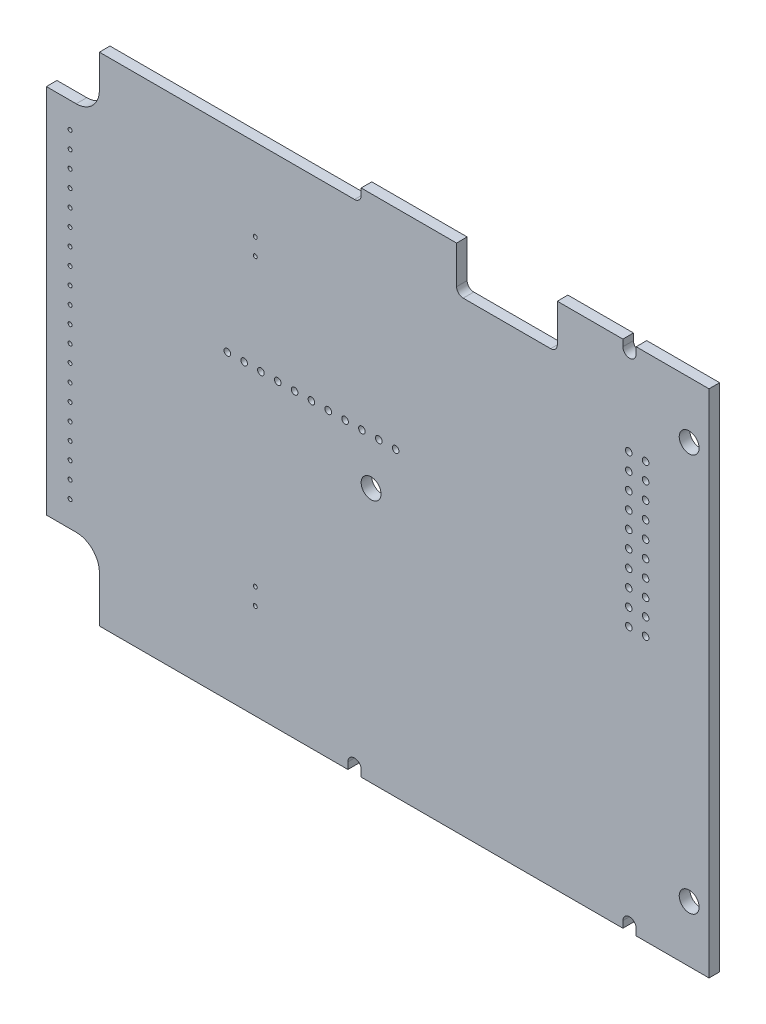
SolidWorks part; units mm, degrees
ref_plane "Płaszczyzna przednia" through (0, 0, 0) normal (0, 0, 1) x (1, 0, 0)
ref_plane "Płaszczyzna górna" through (0, 0, 0) normal (0, 1, 0) x (1, 0, 0)
ref_plane "Płaszczyzna prawa" through (0, 0, 0) normal (1, 0, 0) x (0, 0, -1)
sketch "Geometry Import" plane through (0, 0, 0) normal (0, 0, 1) x (1, 0, 0)
  line L0 (246.9504, 64.1305) -> (246.9504, 64.6805) construction
  line L1 (245.4504, 64.6805) -> (245.4504, 64.1305) construction
  line L2 (245.4504, 64.1305) -> (246.9504, 64.1305) construction
  line L3 (245.4504, 64.1305) -> (245.4504, 63.0305) construction
  line L4 (245.9504, 62.5305) -> (246.9504, 62.5305) construction
  line L5 (246.9504, 62.5305) -> (246.9504, 64.1305) construction
  line L6 (246.9504, 64.1305) -> (245.4504, 64.1305) construction
  line L7 (293.2004, 64.1305) -> (293.2004, 64.6805) construction
  line L8 (291.7004, 64.6805) -> (291.7004, 64.1305) construction
  line L9 (291.7004, 64.1305) -> (293.2004, 64.1305) construction
  line L10 (291.7004, 63.1805) -> (293.2004, 63.1805) construction
  line L11 (293.2004, 63.1805) -> (293.2004, 64.1305) construction
  line L12 (293.2004, 64.1305) -> (291.7004, 64.1305) construction
  line L13 (291.7004, 64.1305) -> (291.7004, 63.1805) construction
  line L14 (334.7004, 64.1305) -> (334.7004, 64.6805) construction
  line L15 (333.2004, 64.6805) -> (333.2004, 64.1305) construction
  line L16 (333.2004, 64.1305) -> (334.7004, 64.1305) construction
  line L17 (333.2004, 63.1805) -> (334.7004, 63.1805) construction
  line L18 (334.7004, 63.1805) -> (334.7004, 64.1305) construction
  line L19 (334.7004, 64.1305) -> (333.2004, 64.1305) construction
  line L20 (333.2004, 64.1305) -> (333.2004, 63.1805) construction
  line L21 (376.2004, 64.1305) -> (376.2004, 64.6805) construction
  line L22 (374.7004, 64.6805) -> (374.7004, 64.1305) construction
  line L23 (374.7004, 64.1305) -> (376.2004, 64.1305) construction
  line L24 (374.7004, 63.1805) -> (376.2004, 63.1805) construction
  line L25 (376.2004, 63.1805) -> (376.2004, 64.1305) construction
  line L26 (376.2004, 64.1305) -> (374.7004, 64.1305) construction
  line L27 (374.7004, 64.1305) -> (374.7004, 63.1805) construction
  line L28 (393.4504, 57.9305) -> (393.4504, 56.4305) construction
  line L29 (393.4504, 56.4305) -> (394.4004, 56.4305) construction
  line L30 (394.4004, 56.4305) -> (394.4004, 57.9305) construction
  line L31 (394.4004, 57.9305) -> (393.4504, 57.9305) construction
  line L32 (394.4004, 56.4305) -> (394.9504, 56.4305) construction
  line L33 (394.9504, 57.9305) -> (394.4004, 57.9305) construction
  line L34 (394.4004, 57.9305) -> (394.4004, 56.4305) construction
  line L35 (394.4004, -6.5695) -> (394.9504, -6.5695) construction
  line L36 (394.9504, -5.0695) -> (394.4004, -5.0695) construction
  line L37 (394.4004, -5.0695) -> (394.4004, -6.5695) construction
  line L38 (393.4504, -5.0695) -> (393.4504, -6.5695) construction
  line L39 (393.4504, -6.5695) -> (394.4004, -6.5695) construction
  line L40 (394.4004, -6.5695) -> (394.4004, -5.0695) construction
  line L41 (394.4004, -5.0695) -> (393.4504, -5.0695) construction
  line L42 (376.2004, -11.8195) -> (374.7004, -11.8195) construction
  line L43 (374.7004, -11.8195) -> (374.7004, -12.7695) construction
  line L44 (374.7004, -12.7695) -> (376.2004, -12.7695) construction
  line L45 (376.2004, -12.7695) -> (376.2004, -11.8195) construction
  line L46 (374.7004, -12.7695) -> (374.7004, -13.3195) construction
  line L47 (376.2004, -13.3195) -> (376.2004, -12.7695) construction
  line L48 (376.2004, -12.7695) -> (374.7004, -12.7695) construction
  line L49 (334.7004, -11.8195) -> (333.2004, -11.8195) construction
  line L50 (333.2004, -11.8195) -> (333.2004, -12.7695) construction
  line L51 (333.2004, -12.7695) -> (334.7004, -12.7695) construction
  line L52 (334.7004, -12.7695) -> (334.7004, -11.8195) construction
  line L53 (333.2004, -12.7695) -> (333.2004, -13.3195) construction
  line L54 (334.7004, -13.3195) -> (334.7004, -12.7695) construction
  line L55 (334.7004, -12.7695) -> (333.2004, -12.7695) construction
  line L56 (293.2004, -11.8195) -> (291.7004, -11.8195) construction
  line L57 (291.7004, -11.8195) -> (291.7004, -12.7695) construction
  line L58 (291.7004, -12.7695) -> (293.2004, -12.7695) construction
  line L59 (293.2004, -12.7695) -> (293.2004, -11.8195) construction
  line L60 (291.7004, -12.7695) -> (291.7004, -13.3195) construction
  line L61 (293.2004, -13.3195) -> (293.2004, -12.7695) construction
  line L62 (293.2004, -12.7695) -> (291.7004, -12.7695) construction
  line L63 (245.4504, -12.7695) -> (245.4504, -13.3195) construction
  line L64 (246.9504, -13.3195) -> (246.9504, -12.7695) construction
  line L65 (246.9504, -12.7695) -> (245.4504, -12.7695) construction
  line L66 (246.9504, -11.1695) -> (245.9504, -11.1695) construction
  line L67 (245.4504, -11.6695) -> (245.4504, -12.7695) construction
  line L68 (245.4504, -12.7695) -> (246.9504, -12.7695) construction
  line L69 (246.9504, -12.7695) -> (246.9504, -11.1695) construction
  line L70 (307.8504, 66.3305) -> (307.8504, 64.6805) construction
  line L71 (307.8504, 64.6805) -> (323.0504, 64.6805) construction
  line L72 (323.0504, 64.6805) -> (323.0504, 66.3305) construction
  line L73 (323.0504, 66.3305) -> (307.8504, 66.3305) construction
  line L74 (307.8504, 64.6805) -> (307.8504, 65.8305) construction
  line L75 (307.8504, 65.8305) -> (293.2004, 65.8305) construction
  line L76 (293.2004, 65.8305) -> (291.7004, 65.8305) construction
  line L77 (291.7004, 65.8305) -> (246.9504, 65.8305) construction
  line L78 (246.9504, 65.8305) -> (245.4504, 65.8305) construction
  line L79 (245.4504, 65.8305) -> (245.4504, 64.6805) construction
  line L80 (246.9504, 64.6805) -> (291.7004, 64.6805) construction
  line L81 (293.2004, 64.6805) -> (307.8504, 64.6805) construction
  line L82 (333.2004, 65.8305) -> (323.0504, 65.8305) construction
  line L83 (323.0504, 65.8305) -> (323.0504, 64.6805) construction
  line L84 (323.0504, 64.6805) -> (333.2004, 64.6805) construction
  line L85 (334.7004, 64.6805) -> (374.7004, 64.6805) construction
  line L86 (376.2004, 64.6805) -> (390.9504, 64.6805) construction
  line L87 (394.9504, 60.6805) -> (394.9504, 57.9305) construction
  line L88 (394.9504, 56.4305) -> (394.9504, -5.0695) construction
  line L89 (394.9504, -6.5695) -> (394.9504, -9.3195) construction
  line L90 (390.9504, -13.3195) -> (376.2004, -13.3195) construction
  line L91 (374.7004, -13.3195) -> (334.7004, -13.3195) construction
  line L92 (333.2004, -13.3195) -> (293.2004, -13.3195) construction
  line L93 (291.7004, -13.3195) -> (246.9504, -13.3195) construction
  line L94 (245.4504, -13.3195) -> (245.4504, -14.4695) construction
  line L95 (245.4504, -14.4695) -> (246.9504, -14.4695) construction
  line L96 (246.9504, -14.4695) -> (291.7004, -14.4695) construction
  line L97 (291.7004, -14.4695) -> (293.2004, -14.4695) construction
  line L98 (293.2004, -14.4695) -> (333.2004, -14.4695) construction
  line L99 (333.2004, -14.4695) -> (334.7004, -14.4695) construction
  line L100 (334.7004, -14.4695) -> (374.7004, -14.4695) construction
  line L101 (374.7004, -14.4695) -> (376.2004, -14.4695) construction
  line L102 (376.2004, -14.4695) -> (390.9504, -14.4695) construction
  line L103 (396.1004, -9.3195) -> (396.1004, -6.5695) construction
  line L104 (396.1004, -6.5695) -> (396.1004, -5.0695) construction
  line L105 (396.1004, -5.0695) -> (396.1004, 56.4305) construction
  line L106 (396.1004, 56.4305) -> (396.1004, 57.9305) construction
  line L107 (396.1004, 57.9305) -> (396.1004, 60.6805) construction
  line L108 (390.9504, 65.8305) -> (376.2004, 65.8305) construction
  line L109 (376.2004, 65.8305) -> (374.7004, 65.8305) construction
  line L110 (374.7004, 65.8305) -> (334.7004, 65.8305) construction
  line L111 (334.7004, 65.8305) -> (333.2004, 65.8305) construction
  line L112 (246.9504, 64.1305) -> (246.9504, 64.6805) construction
  line L113 (245.4504, 64.6805) -> (245.4504, 64.1305) construction
  line L114 (245.4504, 64.1305) -> (246.9504, 64.1305) construction
  line L115 (245.4504, 64.1305) -> (245.4504, 63.0305) construction
  line L116 (245.9504, 62.5305) -> (246.9504, 62.5305) construction
  line L117 (246.9504, 62.5305) -> (246.9504, 64.1305) construction
  line L118 (246.9504, 64.1305) -> (245.4504, 64.1305) construction
  line L119 (293.2004, 64.1305) -> (293.2004, 64.6805) construction
  line L120 (291.7004, 64.6805) -> (291.7004, 64.1305) construction
  line L121 (291.7004, 64.1305) -> (293.2004, 64.1305) construction
  line L122 (291.7004, 63.1805) -> (293.2004, 63.1805) construction
  line L123 (293.2004, 63.1805) -> (293.2004, 64.1305) construction
  line L124 (293.2004, 64.1305) -> (291.7004, 64.1305) construction
  line L125 (291.7004, 64.1305) -> (291.7004, 63.1805) construction
  line L126 (334.7004, 64.1305) -> (334.7004, 64.6805) construction
  line L127 (333.2004, 64.6805) -> (333.2004, 64.1305) construction
  line L128 (333.2004, 64.1305) -> (334.7004, 64.1305) construction
  line L129 (333.2004, 63.1805) -> (334.7004, 63.1805) construction
  line L130 (334.7004, 63.1805) -> (334.7004, 64.1305) construction
  line L131 (334.7004, 64.1305) -> (333.2004, 64.1305) construction
  line L132 (333.2004, 64.1305) -> (333.2004, 63.1805) construction
  line L133 (376.2004, 64.1305) -> (376.2004, 64.6805) construction
  line L134 (374.7004, 64.6805) -> (374.7004, 64.1305) construction
  line L135 (374.7004, 64.1305) -> (376.2004, 64.1305) construction
  line L136 (374.7004, 63.1805) -> (376.2004, 63.1805) construction
  line L137 (376.2004, 63.1805) -> (376.2004, 64.1305) construction
  line L138 (376.2004, 64.1305) -> (374.7004, 64.1305) construction
  line L139 (374.7004, 64.1305) -> (374.7004, 63.1805) construction
  line L140 (393.4504, 57.9305) -> (393.4504, 56.4305) construction
  line L141 (393.4504, 56.4305) -> (394.4004, 56.4305) construction
  line L142 (394.4004, 56.4305) -> (394.4004, 57.9305) construction
  line L143 (394.4004, 57.9305) -> (393.4504, 57.9305) construction
  line L144 (394.4004, 56.4305) -> (394.9504, 56.4305) construction
  line L145 (394.9504, 57.9305) -> (394.4004, 57.9305) construction
  line L146 (394.4004, 57.9305) -> (394.4004, 56.4305) construction
  line L147 (394.4004, -6.5695) -> (394.9504, -6.5695) construction
  line L148 (394.9504, -5.0695) -> (394.4004, -5.0695) construction
  line L149 (394.4004, -5.0695) -> (394.4004, -6.5695) construction
  line L150 (393.4504, -5.0695) -> (393.4504, -6.5695) construction
  line L151 (393.4504, -6.5695) -> (394.4004, -6.5695) construction
  line L152 (394.4004, -6.5695) -> (394.4004, -5.0695) construction
  line L153 (394.4004, -5.0695) -> (393.4504, -5.0695) construction
  line L154 (376.2004, -11.8195) -> (374.7004, -11.8195) construction
  line L155 (374.7004, -11.8195) -> (374.7004, -12.7695) construction
  line L156 (374.7004, -12.7695) -> (376.2004, -12.7695) construction
  line L157 (376.2004, -12.7695) -> (376.2004, -11.8195) construction
  line L158 (374.7004, -12.7695) -> (374.7004, -13.3195) construction
  line L159 (376.2004, -13.3195) -> (376.2004, -12.7695) construction
  line L160 (376.2004, -12.7695) -> (374.7004, -12.7695) construction
  line L161 (334.7004, -11.8195) -> (333.2004, -11.8195) construction
  line L162 (333.2004, -11.8195) -> (333.2004, -12.7695) construction
  line L163 (333.2004, -12.7695) -> (334.7004, -12.7695) construction
  line L164 (334.7004, -12.7695) -> (334.7004, -11.8195) construction
  line L165 (333.2004, -12.7695) -> (333.2004, -13.3195) construction
  line L166 (334.7004, -13.3195) -> (334.7004, -12.7695) construction
  line L167 (334.7004, -12.7695) -> (333.2004, -12.7695) construction
  line L168 (293.2004, -11.8195) -> (291.7004, -11.8195) construction
  line L169 (291.7004, -11.8195) -> (291.7004, -12.7695) construction
  line L170 (291.7004, -12.7695) -> (293.2004, -12.7695) construction
  line L171 (293.2004, -12.7695) -> (293.2004, -11.8195) construction
  line L172 (291.7004, -12.7695) -> (291.7004, -13.3195) construction
  line L173 (293.2004, -13.3195) -> (293.2004, -12.7695) construction
  line L174 (293.2004, -12.7695) -> (291.7004, -12.7695) construction
  line L175 (245.4504, -12.7695) -> (245.4504, -13.3195) construction
  line L176 (246.9504, -13.3195) -> (246.9504, -12.7695) construction
  line L177 (246.9504, -12.7695) -> (245.4504, -12.7695) construction
  line L178 (246.9504, -11.1695) -> (245.9504, -11.1695) construction
  line L179 (245.4504, -11.6695) -> (245.4504, -12.7695) construction
  line L180 (245.4504, -12.7695) -> (246.9504, -12.7695) construction
  line L181 (246.9504, -12.7695) -> (246.9504, -11.1695) construction
  line L182 (307.8504, 66.3305) -> (307.8504, 64.6805) construction
  line L183 (307.8504, 64.6805) -> (323.0504, 64.6805) construction
  line L184 (323.0504, 64.6805) -> (323.0504, 66.3305) construction
  line L185 (323.0504, 66.3305) -> (307.8504, 66.3305) construction
  line L186 (307.8504, 64.6805) -> (307.8504, 65.8305) construction
  line L187 (307.8504, 65.8305) -> (293.2004, 65.8305) construction
  line L188 (293.2004, 65.8305) -> (291.7004, 65.8305) construction
  line L189 (291.7004, 65.8305) -> (246.9504, 65.8305) construction
  line L190 (246.9504, 65.8305) -> (245.4504, 65.8305) construction
  line L191 (245.4504, 65.8305) -> (245.4504, 64.6805) construction
  line L192 (246.9504, 64.6805) -> (291.7004, 64.6805) construction
  line L193 (293.2004, 64.6805) -> (307.8504, 64.6805) construction
  line L194 (333.2004, 65.8305) -> (323.0504, 65.8305) construction
  line L195 (323.0504, 65.8305) -> (323.0504, 64.6805) construction
  line L196 (323.0504, 64.6805) -> (333.2004, 64.6805) construction
  line L197 (334.7004, 64.6805) -> (374.7004, 64.6805) construction
  line L198 (376.2004, 64.6805) -> (390.9504, 64.6805) construction
  line L199 (394.9504, 60.6805) -> (394.9504, 57.9305) construction
  line L200 (394.9504, 56.4305) -> (394.9504, -5.0695) construction
  line L201 (394.9504, -6.5695) -> (394.9504, -9.3195) construction
  line L202 (390.9504, -13.3195) -> (376.2004, -13.3195) construction
  line L203 (374.7004, -13.3195) -> (334.7004, -13.3195) construction
  line L204 (333.2004, -13.3195) -> (293.2004, -13.3195) construction
  line L205 (291.7004, -13.3195) -> (246.9504, -13.3195) construction
  line L206 (245.4504, -13.3195) -> (245.4504, -14.4695) construction
  line L207 (245.4504, -14.4695) -> (246.9504, -14.4695) construction
  line L208 (246.9504, -14.4695) -> (291.7004, -14.4695) construction
  line L209 (291.7004, -14.4695) -> (293.2004, -14.4695) construction
  line L210 (293.2004, -14.4695) -> (333.2004, -14.4695) construction
  line L211 (333.2004, -14.4695) -> (334.7004, -14.4695) construction
  line L212 (334.7004, -14.4695) -> (374.7004, -14.4695) construction
  line L213 (374.7004, -14.4695) -> (376.2004, -14.4695) construction
  line L214 (376.2004, -14.4695) -> (390.9504, -14.4695) construction
  line L215 (396.1004, -9.3195) -> (396.1004, -6.5695) construction
  line L216 (396.1004, -6.5695) -> (396.1004, -5.0695) construction
  line L217 (396.1004, -5.0695) -> (396.1004, 56.4305) construction
  line L218 (396.1004, 56.4305) -> (396.1004, 57.9305) construction
  line L219 (396.1004, 57.9305) -> (396.1004, 60.6805) construction
  line L220 (390.9504, 65.8305) -> (376.2004, 65.8305) construction
  line L221 (376.2004, 65.8305) -> (374.7004, 65.8305) construction
  line L222 (374.7004, 65.8305) -> (334.7004, 65.8305) construction
  line L223 (334.7004, 65.8305) -> (333.2004, 65.8305) construction
  line L228 (243.4504, 60.5183) -> (243.4504, -9.4817)
  line L229 (243.4504, -9.4817) -> (245.4504, -9.4817)
  line L230 (245.4504, -9.4817) -> (245.4504, 60.5183)
  line L231 (245.4504, 60.5183) -> (243.4504, 60.5183)
  line L232 (243.4504, 60.5183) -> (243.4504, -9.4817) construction
  line L233 (243.4504, -9.4817) -> (245.4504, -9.4817) construction
  line L234 (245.4504, -9.4817) -> (245.4504, 60.5183) construction
  line L235 (245.4504, 60.5183) -> (243.4504, 60.5183) construction
  line L240 (317.8504, 58.7305) -> (317.8504, 63.2305)
  line L241 (317.8504, 63.2305) -> (307.8504, 63.2305)
  line L242 (307.8504, 63.2305) -> (307.8504, 58.7305)
  line L243 (307.8504, 58.7305) -> (311.3504, 58.7305)
  line L244 (311.3504, 58.7305) -> (311.3504, 62.7305)
  line L245 (311.3504, 62.7305) -> (314.3504, 62.7305)
  line L246 (314.3504, 62.7305) -> (314.3504, 58.7305)
  line L247 (314.3504, 58.7305) -> (317.8504, 58.7305)
  line L248 (317.8504, 58.7305) -> (317.8504, 63.2305) construction
  line L249 (317.8504, 63.2305) -> (307.8504, 63.2305) construction
  line L250 (307.8504, 63.2305) -> (307.8504, 58.7305) construction
  line L251 (307.8504, 58.7305) -> (311.3504, 58.7305) construction
  line L252 (311.3504, 58.7305) -> (311.3504, 62.7305) construction
  line L253 (311.3504, 62.7305) -> (314.3504, 62.7305) construction
  line L254 (314.3504, 62.7305) -> (314.3504, 58.7305) construction
  line L255 (314.3504, 58.7305) -> (317.8504, 58.7305) construction
  circle A0 centre (250.4504, 57.1805) radius 3 construction
  circle A1 centre (250.4504, 57.1805) radius 1.2 construction
  circle A2 centre (250.4504, -5.8195) radius 1.2 construction
  circle A3 centre (250.4504, -5.8195) radius 3 construction
  circle A4 centre (294.9504, 25.6805) radius 2.5 construction
  circle A5 centre (294.9504, 25.6805) radius 1 construction
  circle A6 centre (342.9504, -4.3195) radius 2.5 construction
  circle A7 centre (342.9504, -4.3195) radius 1 construction
  circle A8 centre (375.4504, -5.8195) radius 3 construction
  circle A9 centre (375.4504, -5.8195) radius 1.2 construction
  circle A10 centre (342.9504, 55.6805) radius 2.5 construction
  circle A11 centre (342.9504, 55.6805) radius 1 construction
  circle A12 centre (375.4504, 57.1805) radius 1.2 construction
  circle A13 centre (375.4504, 57.1805) radius 3 construction
  circle A14 centre (250.4504, 57.1805) radius 3 construction
  circle A15 centre (250.4504, 57.1805) radius 1.2 construction
  circle A16 centre (250.4504, -5.8195) radius 1.2 construction
  circle A17 centre (250.4504, -5.8195) radius 3 construction
  circle A18 centre (294.9504, 25.6805) radius 2.5 construction
  circle A19 centre (294.9504, 25.6805) radius 1 construction
  circle A20 centre (342.9504, -4.3195) radius 2.5 construction
  circle A21 centre (342.9504, -4.3195) radius 1 construction
  circle A22 centre (375.4504, -5.8195) radius 3 construction
  circle A23 centre (375.4504, -5.8195) radius 1.2 construction
  circle A24 centre (342.9504, 55.6805) radius 2.5 construction
  circle A25 centre (342.9504, 55.6805) radius 1 construction
  circle A26 centre (375.4504, 57.1805) radius 1.2 construction
  circle A27 centre (375.4504, 57.1805) radius 3 construction
  arc A28 (245.4504, 63.0305) -> (245.9504, 62.5305) centre (245.9504, 63.0305) ccw construction
  arc A29 (245.9504, -11.1695) -> (245.4504, -11.6695) centre (245.9504, -11.6695) ccw construction
  arc A30 (394.9504, 60.6805) -> (390.9504, 64.6805) centre (390.9504, 60.6805) ccw construction
  arc A31 (390.9504, -13.3195) -> (394.9504, -9.3195) centre (390.9504, -9.3195) ccw construction
  arc A32 (390.9504, -14.4695) -> (396.1004, -9.3195) centre (390.9504, -9.3195) ccw construction
  arc A33 (396.1004, 60.6805) -> (390.9504, 65.8305) centre (390.9504, 60.6805) ccw construction
  arc A34 (245.4504, 63.0305) -> (245.9504, 62.5305) centre (245.9504, 63.0305) ccw construction
  arc A35 (245.9504, -11.1695) -> (245.4504, -11.6695) centre (245.9504, -11.6695) ccw construction
  arc A36 (394.9504, 60.6805) -> (390.9504, 64.6805) centre (390.9504, 60.6805) ccw construction
  arc A37 (390.9504, -13.3195) -> (394.9504, -9.3195) centre (390.9504, -9.3195) ccw construction
  arc A38 (390.9504, -14.4695) -> (396.1004, -9.3195) centre (390.9504, -9.3195) ccw construction
  arc A39 (396.1004, 60.6805) -> (390.9504, 65.8305) centre (390.9504, 60.6805) ccw construction
  dimension "D1" = 0
  dimension "D2" = 0
sketch "Board Outline" plane through (0, 0, 0) normal (0, 0, 1) x (1, 0, 0)
  line L0 (394.9504, -5.0695) -> (394.4004, -5.0695) construction
  line L5 (394.4004, -5.0695) -> (393.4504, -5.0695) construction
  line L6 (393.4504, -5.0695) -> (393.4504, -6.5695) construction
  line L7 (393.4504, -6.5695) -> (394.4004, -6.5695) construction
  line L8 (394.4004, -6.5695) -> (394.9504, -6.5695) construction
  line L9 (394.9504, -6.5695) -> (394.9504, -9.3195) construction
  line L10 (390.9504, -13.3195) -> (376.2004, -13.3195) construction
  line L11 (376.2004, -13.3195) -> (376.2004, -12.7695) construction
  line L12 (376.2004, -12.7695) -> (376.2004, -11.8195) construction
  line L13 (376.2004, -11.8195) -> (374.7004, -11.8195) construction
  line L14 (374.7004, -11.8195) -> (374.7004, -12.7695) construction
  line L15 (374.7004, -12.7695) -> (374.7004, -13.3195) construction
  line L16 (374.7004, -13.3195) -> (334.7004, -13.3195) construction
  line L17 (334.7004, -13.3195) -> (334.7004, -12.7695) construction
  line L18 (334.7004, -12.7695) -> (334.7004, -11.8195) construction
  line L19 (334.7004, -11.8195) -> (333.2004, -11.8195) construction
  line L20 (333.2004, -11.8195) -> (333.2004, -12.7695) construction
  line L21 (333.2004, -12.7695) -> (333.2004, -13.3195) construction
  line L22 (333.2004, -13.3195) -> (293.2004, -13.3195) construction
  line L23 (293.2004, -13.3195) -> (293.2004, -12.7695) construction
  line L24 (293.2004, -12.7695) -> (293.2004, -11.8195) construction
  line L25 (293.2004, -11.8195) -> (291.7004, -11.8195) construction
  line L26 (291.7004, -11.8195) -> (291.7004, -12.7695) construction
  line L27 (291.7004, -12.7695) -> (291.7004, -13.3195) construction
  line L28 (291.7004, -13.3195) -> (246.9504, -13.3195) construction
  line L29 (246.9504, -13.3195) -> (246.9504, -12.7695) construction
  line L30 (246.9504, -12.7695) -> (246.9504, -11.1695) construction
  line L31 (246.9504, -11.1695) -> (245.9504, -11.1695) construction
  line L32 (245.4504, -9.4817) -> (245.4504, 60.5183) construction
  line L33 (246.9504, 62.5305) -> (246.9504, 64.1305) construction
  line L34 (245.9504, 62.5305) -> (246.9504, 62.5305) construction
  line L35 (246.9504, 64.1305) -> (246.9504, 64.6805) construction
  line L36 (314.3504, 58.7305) -> (317.8504, 58.7305) construction
  line L37 (307.8504, 58.7305) -> (311.3504, 58.7305) construction
  line L38 (307.8504, 63.2305) -> (307.8504, 58.7305) construction
  line L39 (246.9504, 64.6805) -> (291.7004, 64.6805) construction
  line L40 (291.7004, 64.6805) -> (291.7004, 64.1305) construction
  line L41 (291.7004, 64.1305) -> (291.7004, 63.1805) construction
  line L42 (291.7004, 63.1805) -> (293.2004, 63.1805) construction
  line L43 (293.2004, 63.1805) -> (293.2004, 64.1305) construction
  line L44 (293.2004, 64.1305) -> (293.2004, 64.6805) construction
  line L45 (293.2004, 64.6805) -> (307.8504, 64.6805) construction
  line L46 (323.0504, 64.6805) -> (333.2004, 64.6805) construction
  line L47 (333.2004, 64.6805) -> (333.2004, 64.1305) construction
  line L48 (333.2004, 64.1305) -> (333.2004, 63.1805) construction
  line L49 (333.2004, 63.1805) -> (334.7004, 63.1805) construction
  line L50 (334.7004, 63.1805) -> (334.7004, 64.1305) construction
  line L51 (334.7004, 64.1305) -> (334.7004, 64.6805) construction
  line L52 (334.7004, 64.6805) -> (374.7004, 64.6805) construction
  line L53 (374.7004, 64.6805) -> (374.7004, 64.1305) construction
  line L54 (374.7004, 64.1305) -> (374.7004, 63.1805) construction
  line L55 (374.7004, 63.1805) -> (376.2004, 63.1805) construction
  line L56 (376.2004, 63.1805) -> (376.2004, 64.1305) construction
  line L57 (376.2004, 64.1305) -> (376.2004, 64.6805) construction
  line L58 (376.2004, 64.6805) -> (390.9504, 64.6805) construction
  line L59 (394.9504, 60.6805) -> (394.9504, 57.9305) construction
  line L60 (394.9504, 57.9305) -> (394.4004, 57.9305) construction
  line L61 (394.4004, 57.9305) -> (393.4504, 57.9305) construction
  line L62 (393.4504, 57.9305) -> (393.4504, 56.4305) construction
  line L63 (393.4504, 56.4305) -> (394.4004, 56.4305) construction
  line L64 (394.4004, 56.4305) -> (394.9504, 56.4305) construction
  line L65 (394.9504, 56.4305) -> (394.9504, -5.0695) construction
  line L66 (394.9504, -5.0695) -> (394.4004, -5.0695) construction
  line L67 (394.4004, -5.0695) -> (393.4504, -5.0695) construction
  line L68 (393.4504, -5.0695) -> (393.4504, -6.5695) construction
  line L69 (393.4504, -6.5695) -> (394.4004, -6.5695) construction
  line L70 (394.4004, -6.5695) -> (394.9504, -6.5695) construction
  line L71 (394.9504, -6.5695) -> (394.9504, -9.3195) construction
  line L72 (390.9504, -13.3195) -> (376.2004, -13.3195) construction
  line L73 (376.2004, -13.3195) -> (376.2004, -12.7695) construction
  line L74 (376.2004, -12.7695) -> (376.2004, -11.8195) construction
  line L75 (376.2004, -11.8195) -> (374.7004, -11.8195) construction
  line L76 (374.7004, -11.8195) -> (374.7004, -12.7695) construction
  line L77 (374.7004, -12.7695) -> (374.7004, -13.3195) construction
  line L78 (374.7004, -13.3195) -> (334.7004, -13.3195) construction
  line L79 (334.7004, -13.3195) -> (334.7004, -12.7695) construction
  line L80 (334.7004, -12.7695) -> (334.7004, -11.8195) construction
  line L81 (334.7004, -11.8195) -> (333.2004, -11.8195) construction
  line L82 (333.2004, -11.8195) -> (333.2004, -12.7695) construction
  line L83 (333.2004, -12.7695) -> (333.2004, -13.3195) construction
  line L84 (333.2004, -13.3195) -> (293.2004, -13.3195) construction
  line L85 (293.2004, -13.3195) -> (293.2004, -12.481) construction
  line L86 (293.2004, -12.7695) -> (293.2004, -11.8195) construction
  line L87 (293.2004, -11.8195) -> (291.7004, -11.8195) construction
  line L88 (291.7004, -11.8195) -> (291.7004, -12.7695) construction
  line L89 (291.7004, -12.7695) -> (291.7004, -13.3195) construction
  line L90 (291.7004, -13.3195) -> (246.9504, -13.3195) construction
  line L91 (246.9504, -13.3195) -> (246.9504, -12.7695) construction
  line L92 (246.9504, -12.7695) -> (246.9504, -11.1695) construction
  line L93 (246.9504, -11.1695) -> (245.9504, -11.1695) construction
  line L94 (245.4504, -9.4817) -> (245.4504, 60.5183) construction
  line L95 (246.9504, 62.5305) -> (246.9504, 64.1305) construction
  line L96 (245.9504, 62.5305) -> (246.9504, 62.5305) construction
  line L97 (246.9504, 64.1305) -> (246.9504, 64.6805) construction
  line L98 (314.3504, 58.7305) -> (323.0504, 58.7305) construction
  line L99 (307.8504, 58.7305) -> (314.3504, 58.7305) construction
  line L100 (307.8504, 64.6805) -> (307.8504, 58.7305) construction
  line L101 (246.9504, 64.6805) -> (291.7004, 64.6805) construction
  line L102 (291.7004, 64.6805) -> (291.7004, 64.1305) construction
  line L103 (291.7004, 64.1305) -> (291.7004, 63.1805) construction
  line L104 (291.7004, 63.1805) -> (293.2004, 63.1805) construction
  line L105 (293.2004, 63.1805) -> (293.2004, 64.1305) construction
  line L106 (293.2004, 64.1305) -> (293.2004, 64.6805) construction
  line L107 (293.2004, 64.6805) -> (307.8504, 64.6805) construction
  line L108 (323.0504, 64.6805) -> (333.2004, 64.6805) construction
  line L109 (333.2004, 64.6805) -> (333.2004, 64.1305) construction
  line L110 (333.2004, 64.1305) -> (333.2004, 63.1805) construction
  line L111 (333.2004, 63.1805) -> (334.7004, 63.1805) construction
  line L112 (334.7004, 63.1805) -> (334.7004, 64.1305) construction
  line L113 (334.7004, 64.1305) -> (334.7004, 64.6805) construction
  line L114 (334.7004, 64.6805) -> (374.7004, 64.6805) construction
  line L115 (374.7004, 64.6805) -> (374.7004, 64.1305) construction
  line L116 (374.7004, 64.1305) -> (374.7004, 63.1805) construction
  line L117 (374.7004, 63.1805) -> (376.2004, 63.1805) construction
  line L118 (376.2004, 63.1805) -> (376.2004, 64.1305) construction
  line L119 (376.2004, 64.1305) -> (376.2004, 64.6805) construction
  line L120 (376.2004, 64.6805) -> (390.9504, 64.6805) construction
  line L121 (394.9504, 60.6805) -> (394.9504, 57.9305) construction
  line L122 (394.9504, 57.9305) -> (394.4004, 57.9305) construction
  line L123 (394.4004, 57.9305) -> (393.4504, 57.9305) construction
  line L124 (393.4504, 57.9305) -> (393.4504, 56.4305) construction
  line L125 (393.4504, 56.4305) -> (394.4004, 56.4305) construction
  line L126 (394.4004, 56.4305) -> (394.9504, 56.4305) construction
  line L127 (394.9504, 56.4305) -> (394.9504, -5.0695) construction
  line L128 (245.9504, 62.5305) -> (245.4504, 62.5305) construction
  line L129 (245.4504, 62.5305) -> (245.4504, 60.5183) construction
  line L130 (245.4504, -9.4817) -> (245.4504, -11.1695) construction
  line L131 (245.4504, -11.1695) -> (245.9504, -11.1695) construction
  line L132 (323.0504, 64.6805) -> (323.0504, 58.7305) construction
  line L133 (394.4504, 53.6805) -> (394.4504, -2.3195)
  line L134 (376.2004, 64.1805) -> (390.9504, 64.1805) construction
  line L135 (394.4504, 60.6805) -> (394.4504, 57.9305) construction
  line L136 (334.9504, 64.1805) -> (371.9504, 64.1805)
  line L137 (323.0504, 64.1805) -> (332.9504, 64.1805)
  line L138 (293.4504, 64.1805) -> (307.8504, 64.1805)
  line L139 (291.4504, 64.1805) -> (292.4504, 64.1805) construction
  line L140 (291.7004, -12.8195) -> (292.4504, -12.8195) construction
  line L141 (333.2004, -12.8195) -> (333.9504, -12.8195) construction
  line L142 (371.9504, -12.8195) -> (334.9504, -12.8195)
  line L143 (394.4504, -6.5695) -> (394.4504, -9.3195) construction
  line L144 (390.9504, -12.8195) -> (376.2004, -12.8195) construction
  line L145 (245.9504, -2.3195) -> (245.9504, 53.6805)
  line L146 (250.4504, 53.6805) -> (245.9504, 53.6805)
  line L147 (253.9504, 57.1805) -> (253.9504, 62.1805)
  line L148 (250.4504, -2.3195) -> (245.9504, -2.3195)
  line L149 (253.9504, -5.8195) -> (253.9504, -12.8195)
  line L150 (245.9504, -9.4817) -> (245.9504, -2.3195) construction
  line L151 (245.9504, -9.4817) -> (245.9504, 60.5183) construction
  line L152 (253.9504, -12.8195) -> (246.9504, -12.8195) construction
  line L153 (291.7004, -12.8195) -> (246.9504, -12.8195) construction
  line L154 (245.9504, 53.6805) -> (245.9504, 60.5183) construction
  line L155 (246.9504, 64.1805) -> (253.9504, 64.1805) construction
  line L156 (246.9504, 64.1805) -> (291.7004, 64.1805) construction
  line L157 (307.8504, 64.1805) -> (307.8504, 58.4805)
  line L158 (323.0504, 64.1805) -> (323.0504, 58.4805)
  line L159 (308.8504, 57.4805) -> (322.0504, 57.4805)
  line L160 (293.4504, 63.1805) -> (293.4504, 64.1805)
  line L161 (291.4504, 63.1805) -> (291.4504, 64.1805) construction
  line L162 (292.4504, 62.1805) -> (253.9504, 62.1805)
  line L163 (253.9504, 62.1805) -> (253.9504, 64.1805) construction
  line L164 (253.9504, 64.1805) -> (291.4504, 64.1805) construction
  line L165 (292.4504, 64.1805) -> (291.7004, 64.1805) construction
  line L166 (293.2004, 64.1805) -> (292.4504, 64.1805) construction
  line L167 (293.2004, 64.1805) -> (307.8504, 64.1805) construction
  line L168 (292.4504, 64.1805) -> (293.4504, 64.1805) construction
  line L169 (332.9504, 63.1805) -> (332.9504, 64.1805)
  line L170 (334.9504, 63.1805) -> (334.9504, 64.1805)
  line L171 (332.9504, 64.1805) -> (333.2004, 64.1805) construction
  line L172 (323.0504, 64.1805) -> (333.2004, 64.1805) construction
  line L173 (334.7004, 64.1805) -> (334.9504, 64.1805) construction
  line L174 (334.7004, 64.1805) -> (374.7004, 64.1805) construction
  line L175 (371.9504, 57.1805) -> (371.9504, 64.1805)
  line L176 (375.4504, 53.6805) -> (394.4504, 53.6805)
  line L177 (371.9504, 64.1805) -> (374.7004, 64.1805) construction
  line L178 (394.4504, 56.4305) -> (394.4504, 53.6805) construction
  line L179 (394.4504, 56.4305) -> (394.4504, -5.0695) construction
  line L180 (375.4504, -2.3195) -> (394.4504, -2.3195)
  line L181 (371.9504, -5.8195) -> (371.9504, -12.8195)
  line L182 (374.7004, -12.8195) -> (371.9504, -12.8195) construction
  line L183 (374.7004, -12.8195) -> (334.7004, -12.8195) construction
  line L184 (394.4504, -2.3195) -> (394.4504, -5.0695) construction
  line L185 (332.9504, -11.8195) -> (332.9504, -12.8195)
  line L186 (334.9504, -11.8195) -> (334.9504, -12.8195)
  line L187 (333.9504, -12.8195) -> (332.9504, -12.8195) construction
  line L188 (332.9504, -12.8195) -> (293.4504, -12.8195)
  line L189 (333.2004, -12.8195) -> (293.2004, -12.8195) construction
  line L190 (333.9504, -12.8195) -> (334.7004, -12.8195) construction
  line L191 (334.9504, -12.8195) -> (333.9504, -12.8195) construction
  line L192 (291.4504, -11.8195) -> (291.4504, -12.8195)
  line L193 (293.4504, -11.8195) -> (293.4504, -12.8195)
  line L194 (292.4504, -12.8195) -> (291.4504, -12.8195) construction
  line L195 (291.4504, -12.8195) -> (253.9504, -12.8195)
  line L196 (293.4504, -12.8195) -> (292.4504, -12.8195) construction
  line L197 (292.4504, -12.8195) -> (293.2004, -12.8195) construction
  line L198 (293.2004, -12.481) -> (293.2004, -12.8195) construction
  line L199 (293.2004, -12.8195) -> (293.2004, -12.7695) construction
  arc A0 (390.9504, -13.3195) -> (394.9504, -9.3195) centre (390.9504, -9.3195) ccw construction
  arc A1 (394.9504, 60.6805) -> (390.9504, 64.6805) centre (390.9504, 60.6805) ccw construction
  arc A2 (390.9504, -13.3195) -> (394.9504, -9.3195) centre (390.9504, -9.3195) ccw construction
  arc A3 (394.9504, 60.6805) -> (390.9504, 64.6805) centre (390.9504, 60.6805) ccw construction
  circle A4 centre (375.4504, -5.8195) radius 3 construction
  circle A5 centre (375.4504, 57.1805) radius 3 construction
  circle A6 centre (250.4504, -5.8195) radius 3 construction
  circle A7 centre (250.4504, 57.1805) radius 3 construction
  circle A8 centre (375.4504, -5.8195) radius 3 construction
  circle A9 centre (375.4504, 57.1805) radius 3 construction
  circle A10 centre (250.4504, -5.8195) radius 3 construction
  circle A11 centre (250.4504, 57.1805) radius 3 construction
  circle A12 centre (250.4504, 57.1805) radius 3.5 construction
  circle A13 centre (250.4504, -5.8195) radius 3.5 construction
  circle A14 centre (375.4504, -5.8195) radius 3.5 construction
  circle A15 centre (375.4504, 57.1805) radius 3.5 construction
  arc A16 (394.4504, 60.6805) -> (390.9504, 64.1805) centre (390.9504, 60.6805) ccw construction
  arc A17 (390.9504, -12.8195) -> (394.4504, -9.3195) centre (390.9504, -9.3195) ccw construction
  arc A18 (250.4504, 53.6805) -> (253.9504, 57.1805) centre (250.4504, 57.1805) ccw
  arc A19 (253.9504, -5.8195) -> (250.4504, -2.3195) centre (250.4504, -5.8195) ccw
  arc A20 (307.8504, 58.4805) -> (308.8504, 57.4805) centre (308.8504, 58.4805) ccw
  arc A21 (323.0504, 58.4805) -> (322.0504, 57.4805) centre (322.0504, 58.4805) cw
  arc A22 (292.4504, 62.1805) -> (293.4504, 63.1805) centre (292.4504, 63.1805) ccw
  arc A23 (292.4504, 64.1805) -> (291.4504, 63.1805) centre (292.4504, 63.1805) ccw construction
  arc A24 (291.7004, 63.8419) -> (292.4504, 64.1805) centre (292.4504, 63.1805) ccw construction
  arc A25 (293.2004, 63.8419) -> (291.7004, 63.8419) centre (292.4504, 63.1805) ccw construction
  arc A26 (292.4504, 64.1805) -> (293.2004, 63.8419) centre (292.4504, 63.1805) ccw construction
  arc A27 (293.4504, 63.1805) -> (292.4504, 64.1805) centre (292.4504, 63.1805) ccw construction
  arc A28 (291.4504, 63.1805) -> (292.4504, 62.1805) centre (292.4504, 63.1805) ccw construction
  arc A29 (332.9504, 63.1805) -> (334.9504, 63.1805) centre (333.9504, 63.1805) ccw
  arc A30 (333.2004, 63.8419) -> (332.9504, 63.1805) centre (333.9504, 63.1805) ccw construction
  arc A31 (334.7004, 63.8419) -> (333.2004, 63.8419) centre (333.9504, 63.1805) ccw construction
  arc A32 (334.9504, 63.1805) -> (334.7004, 63.8419) centre (333.9504, 63.1805) ccw construction
  arc A33 (371.9504, 57.1805) -> (375.4504, 53.6805) centre (375.4504, 57.1805) ccw
  arc A34 (371.9504, -5.8195) -> (375.4504, -2.3195) centre (375.4504, -5.8195) cw
  arc A35 (334.7004, -12.481) -> (333.9504, -12.8195) centre (333.9504, -11.8195) ccw construction
  arc A36 (332.9504, -11.8195) -> (333.9504, -12.8195) centre (333.9504, -11.8195) ccw construction
  arc A37 (333.9504, -12.8195) -> (333.2004, -12.481) centre (333.9504, -11.8195) ccw construction
  arc A38 (333.2004, -12.481) -> (334.7004, -12.481) centre (333.9504, -11.8195) ccw construction
  arc A39 (333.9504, -12.8195) -> (334.9504, -11.8195) centre (333.9504, -11.8195) ccw construction
  arc A40 (334.9504, -11.8195) -> (332.9504, -11.8195) centre (333.9504, -11.8195) ccw
  arc A41 (291.7004, -12.481) -> (293.2004, -12.481) centre (292.4504, -11.8195) ccw construction
  arc A42 (291.4504, -11.8195) -> (292.4504, -12.8195) centre (292.4504, -11.8195) ccw construction
  arc A43 (292.4504, -12.8195) -> (291.7004, -12.481) centre (292.4504, -11.8195) ccw construction
  arc A44 (292.4504, -12.8195) -> (293.4504, -11.8195) centre (292.4504, -11.8195) ccw construction
  arc A45 (293.4504, -11.8195) -> (291.4504, -11.8195) centre (292.4504, -11.8195) ccw
  arc A46 (293.2004, -12.481) -> (292.4504, -12.8195) centre (292.4504, -11.8195) ccw construction
  circle A47 centre (292.4504, 63.1805) radius 0.75 construction
  point P139 (292.4504, 63.1805)
  point P153 (333.9504, 63.1805)
  point P168 (333.9504, -11.8195)
  point P178 (292.4504, -11.8195)
  dimension "D5" = 1
  dimension "D6" = 1
  dimension "D4" = 0.5
  dimension "D8" = 1
  dimension "D1" = 0.5
  dimension "D2" = 0.5
  dimension "D3" = 0.5
extrude "Boss-Extrude1" add sketch "Board Outline" along normal blind 1.6
sketch "Sketch3" plane through (0, 0, 1.6) normal (0, 0, 1) x (1, 0, 0)
  circle A0 centre (342.9504, 55.6805) radius 1 construction
  circle A1 centre (342.9504, -4.3195) radius 1 construction
  circle A2 centre (294.9504, 25.6805) radius 1 construction
  circle A3 centre (342.9504, 55.6805) radius 1 construction
  circle A4 centre (342.9504, -4.3195) radius 1 construction
  circle A5 centre (294.9504, 25.6805) radius 1 construction
  circle A6 centre (294.9504, 25.6805) radius 1.5
  circle A7 centre (342.9504, -4.3195) radius 1.5
  circle A8 centre (342.9504, 55.6805) radius 1.5
  dimension "D1" = 3
extrude "Cut-Extrude1" cut sketch "Sketch3" against normal through all
sketch "Sketch4" plane through (0, 0, 1.6) normal (0, 0, 1) x (1, 0, 0)
  line L0 (395.9504, -16.8195) -> (345.9504, -16.8195)
  line L1 (395.9504, -16.8195) -> (395.9504, 68.1805)
  line L2 (345.9504, -16.8195) -> (345.9504, 68.1805)
  line L3 (395.9504, 68.1805) -> (345.9504, 68.1805)
  line L4 (395.9504, -16.8195) -> (345.9504, 68.1805) construction
  line L5 (345.9504, -16.8195) -> (395.9504, 68.1805) construction
  line L6 (394.4504, -2.3195) -> (394.4504, 53.6805) construction
  line L7 (245.9504, 53.6805) -> (245.9504, -2.3195) construction
  point P1 (370.9504, 25.6805)
  point P8 (394.4504, 25.6805)
  dimension "D1" = 100
  dimension "D2" = 50
  dimension "D3" = 85
extrude "Cut-Extrude2" cut sketch "Sketch4" against normal through all
sketch "Sketch5" plane through (0, 0, 1.6) normal (0, 0, 1) x (1, 0, 0)
  line L0 (249.5004, 47.0205) -> (249.5504, 47.0205) construction
  line L1 (249.6504, 47.1205) -> (249.6504, 47.4205) construction
  line L2 (249.5504, 47.5205) -> (249.5004, 47.5205) construction
  line L3 (249.4004, 47.4205) -> (249.4004, 47.1205) construction
  line L4 (249.5004, 49.5605) -> (249.5504, 49.5605)
  line L5 (249.6504, 49.6605) -> (249.6504, 49.9605)
  line L6 (249.5504, 50.0605) -> (249.5004, 50.0605)
  line L7 (249.4004, 49.9605) -> (249.4004, 49.6605)
  line L8 (249.5004, 49.5605) -> (249.5504, 49.5605) construction
  line L9 (249.6504, 49.6605) -> (249.6504, 49.9605) construction
  line L10 (249.5504, 50.0605) -> (249.5004, 50.0605) construction
  line L11 (249.4004, 49.9605) -> (249.4004, 49.6605) construction
  line L12 (277.5004, 4.3405) -> (277.4504, 4.3405) construction
  line L13 (277.3504, 4.2405) -> (277.3504, 3.9405) construction
  line L14 (277.4504, 3.8405) -> (277.5004, 3.8405) construction
  line L15 (277.6004, 3.9405) -> (277.6004, 4.2405) construction
  line L16 (277.5004, 1.8005) -> (277.4504, 1.8005) construction
  line L17 (277.3504, 1.7005) -> (277.3504, 1.4005) construction
  line L18 (277.4504, 1.3005) -> (277.5004, 1.3005) construction
  line L19 (277.6004, 1.4005) -> (277.6004, 1.7005) construction
  line L20 (249.5004, 47.0205) -> (249.5504, 47.0205) construction
  line L21 (249.6504, 47.1205) -> (249.6504, 47.4205) construction
  line L22 (249.5504, 47.5205) -> (249.5004, 47.5205) construction
  line L23 (249.4004, 47.4205) -> (249.4004, 47.1205) construction
  line L24 (277.5004, 4.3405) -> (277.4504, 4.3405) construction
  line L25 (277.3504, 4.2405) -> (277.3504, 3.9405) construction
  line L26 (277.4504, 3.8405) -> (277.5004, 3.8405) construction
  line L27 (277.6004, 3.9405) -> (277.6004, 4.2405) construction
  line L28 (277.5004, 1.8005) -> (277.4504, 1.8005) construction
  line L29 (277.3504, 1.7005) -> (277.3504, 1.4005) construction
  line L30 (277.4504, 1.3005) -> (277.5004, 1.3005) construction
  line L31 (277.6004, 1.4005) -> (277.6004, 1.7005) construction
  line L36 (249.5004, 1.3005) -> (249.5504, 1.3005)
  line L37 (249.6504, 1.4005) -> (249.6504, 1.7005)
  line L38 (249.5504, 1.8005) -> (249.5004, 1.8005)
  line L39 (249.4004, 1.7005) -> (249.4004, 1.4005)
  line L40 (249.5004, 1.3005) -> (249.5504, 1.3005) construction
  line L41 (249.6504, 1.4005) -> (249.6504, 1.7005) construction
  line L42 (249.5504, 1.8005) -> (249.5004, 1.8005) construction
  line L43 (249.4004, 1.7005) -> (249.4004, 1.4005) construction
  arc A0 (249.5504, 47.0205) -> (249.6504, 47.1205) centre (249.5504, 47.1205) ccw construction
  arc A1 (249.6504, 47.4205) -> (249.5504, 47.5205) centre (249.5504, 47.4205) ccw construction
  arc A2 (249.5004, 47.5205) -> (249.4004, 47.4205) centre (249.5004, 47.4205) ccw construction
  arc A3 (249.4004, 47.1205) -> (249.5004, 47.0205) centre (249.5004, 47.1205) ccw construction
  arc A4 (249.5504, 49.5605) -> (249.6504, 49.6605) centre (249.5504, 49.6605) ccw
  arc A5 (249.6504, 49.9605) -> (249.5504, 50.0605) centre (249.5504, 49.9605) ccw
  arc A6 (249.5004, 50.0605) -> (249.4004, 49.9605) centre (249.5004, 49.9605) ccw
  arc A7 (249.4004, 49.6605) -> (249.5004, 49.5605) centre (249.5004, 49.6605) ccw
  arc A8 (249.5504, 49.5605) -> (249.6504, 49.6605) centre (249.5504, 49.6605) ccw construction
  arc A9 (249.6504, 49.9605) -> (249.5504, 50.0605) centre (249.5504, 49.9605) ccw construction
  arc A10 (249.5004, 50.0605) -> (249.4004, 49.9605) centre (249.5004, 49.9605) ccw construction
  arc A11 (249.4004, 49.6605) -> (249.5004, 49.5605) centre (249.5004, 49.6605) ccw construction
  arc A12 (277.4504, 4.3405) -> (277.3504, 4.2405) centre (277.4504, 4.2405) ccw construction
  arc A13 (277.3504, 3.9405) -> (277.4504, 3.8405) centre (277.4504, 3.9405) ccw construction
  arc A14 (277.5004, 3.8405) -> (277.6004, 3.9405) centre (277.5004, 3.9405) ccw construction
  arc A15 (277.6004, 4.2405) -> (277.5004, 4.3405) centre (277.5004, 4.2405) ccw construction
  arc A16 (277.4504, 1.8005) -> (277.3504, 1.7005) centre (277.4504, 1.7005) ccw construction
  arc A17 (277.3504, 1.4005) -> (277.4504, 1.3005) centre (277.4504, 1.4005) ccw construction
  arc A18 (277.5004, 1.3005) -> (277.6004, 1.4005) centre (277.5004, 1.4005) ccw construction
  arc A19 (277.6004, 1.7005) -> (277.5004, 1.8005) centre (277.5004, 1.7005) ccw construction
  arc A20 (249.5504, 47.0205) -> (249.6504, 47.1205) centre (249.5504, 47.1205) ccw construction
  arc A21 (249.6504, 47.4205) -> (249.5504, 47.5205) centre (249.5504, 47.4205) ccw construction
  arc A22 (249.5004, 47.5205) -> (249.4004, 47.4205) centre (249.5004, 47.4205) ccw construction
  arc A23 (249.4004, 47.1205) -> (249.5004, 47.0205) centre (249.5004, 47.1205) ccw construction
  arc A24 (277.4504, 4.3405) -> (277.3504, 4.2405) centre (277.4504, 4.2405) ccw construction
  arc A25 (277.3504, 3.9405) -> (277.4504, 3.8405) centre (277.4504, 3.9405) ccw construction
  arc A26 (277.5004, 3.8405) -> (277.6004, 3.9405) centre (277.5004, 3.9405) ccw construction
  arc A27 (277.6004, 4.2405) -> (277.5004, 4.3405) centre (277.5004, 4.2405) ccw construction
  arc A28 (277.4504, 1.8005) -> (277.3504, 1.7005) centre (277.4504, 1.7005) ccw construction
  arc A29 (277.3504, 1.4005) -> (277.4504, 1.3005) centre (277.4504, 1.4005) ccw construction
  arc A30 (277.5004, 1.3005) -> (277.6004, 1.4005) centre (277.5004, 1.4005) ccw construction
  arc A31 (277.6004, 1.7005) -> (277.5004, 1.8005) centre (277.5004, 1.7005) ccw construction
  circle A32 centre (249.5254, 49.8105) radius 0.2521 construction
  circle A33 centre (249.5254, 49.8105) radius 0.3
  circle A34 centre (277.4754, 49.8105) radius 0.3
  circle A35 centre (277.4754, 47.2705) radius 0.3
  circle A52 centre (277.4754, 4.0905) radius 0.3
  circle A54 centre (249.5254, 47.2705) radius 0.3
  circle A55 centre (249.5254, 44.7305) radius 0.3
  circle A56 centre (249.5254, 42.1905) radius 0.3
  circle A57 centre (249.5254, 39.6505) radius 0.3
  circle A58 centre (249.5254, 37.1105) radius 0.3
  circle A59 centre (249.5254, 34.5705) radius 0.3
  circle A60 centre (249.5254, 32.0305) radius 0.3
  circle A61 centre (249.5254, 29.4905) radius 0.3
  circle A62 centre (249.5254, 26.9505) radius 0.3
  circle A63 centre (249.5254, 24.4105) radius 0.3
  circle A64 centre (249.5254, 21.8705) radius 0.3
  circle A65 centre (249.5254, 19.3305) radius 0.3
  circle A66 centre (249.5254, 16.7905) radius 0.3
  circle A67 centre (249.5254, 14.2505) radius 0.3
  circle A68 centre (249.5254, 11.7105) radius 0.3
  circle A69 centre (249.5254, 9.1705) radius 0.3
  circle A70 centre (249.5254, 6.6305) radius 0.3
  circle A71 centre (249.5254, 4.0905) radius 0.3
  circle A73 centre (277.4754, 44.7305) radius 0.3 [skipped]
  circle A74 centre (277.4754, 42.1905) radius 0.3 [skipped]
  circle A75 centre (277.4754, 39.6505) radius 0.3 [skipped]
  circle A76 centre (277.4754, 37.1105) radius 0.3 [skipped]
  circle A77 centre (277.4754, 34.5705) radius 0.3 [skipped]
  circle A78 centre (277.4754, 32.0305) radius 0.3 [skipped]
  circle A79 centre (277.4754, 29.4905) radius 0.3 [skipped]
  circle A80 centre (277.4754, 26.9505) radius 0.3 [skipped]
  circle A81 centre (277.4754, 24.4105) radius 0.3 [skipped]
  circle A82 centre (277.4754, 21.8705) radius 0.3 [skipped]
  circle A83 centre (277.4754, 19.3305) radius 0.3 [skipped]
  circle A84 centre (277.4754, 16.7905) radius 0.3 [skipped]
  circle A85 centre (277.4754, 14.2505) radius 0.3 [skipped]
  circle A86 centre (277.4754, 11.7105) radius 0.3 [skipped]
  circle A87 centre (277.4754, 9.1705) radius 0.3 [skipped]
  circle A88 centre (277.4754, 6.6305) radius 0.3 [skipped]
  circle A89 centre (249.5254, 1.5505) radius 0.3
  circle A90 centre (277.4754, 1.5505) radius 0.3
  arc A93 (249.5504, 1.3005) -> (249.6504, 1.4005) centre (249.5504, 1.4005) ccw
  arc A94 (249.6504, 1.7005) -> (249.5504, 1.8005) centre (249.5504, 1.7005) ccw
  arc A95 (249.5004, 1.8005) -> (249.4004, 1.7005) centre (249.5004, 1.7005) ccw
  arc A96 (249.4004, 1.4005) -> (249.5004, 1.3005) centre (249.5004, 1.4005) ccw
  arc A97 (249.5504, 1.3005) -> (249.6504, 1.4005) centre (249.5504, 1.4005) ccw construction
  arc A98 (249.6504, 1.7005) -> (249.5504, 1.8005) centre (249.5504, 1.7005) ccw construction
  arc A99 (249.5004, 1.8005) -> (249.4004, 1.7005) centre (249.5004, 1.7005) ccw construction
  arc A100 (249.4004, 1.4005) -> (249.5004, 1.3005) centre (249.5004, 1.4005) ccw construction
  point P22 (249.5254, 50.0605)
  point P25 (249.6504, 49.8105)
  point P31 (249.4004, 49.8105)
  point P35 (249.4004, 47.2705)
  point P37 (277.4754, 1.3005)
  point P60 (249.4004, 1.5505)
  dimension "D2" = 0.6
  dimension "D4" = 2.54
  dimension "D5" = 27.95
  dimension "D6" = 2.54
  dimension "D7" = 27.95
  dimension "D10" = 48.26
  dimension "D1" = 0
  dimension "D9" = 0
  dimension "D8" = 2
  dimension "D3" = 20
extrude "Cut-Extrude3" cut sketch "Sketch5" against normal through all
sketch "Sketch6" plane through (0, 0, 0) normal (0, 0, -1) x (-1, 0, 0)
  circle A0 centre (-333.8344, 49.9035) radius 0.5 construction
  circle A1 centre (-333.8344, 47.3635) radius 0.5 construction
  circle A2 centre (-336.3744, 47.3635) radius 0.5 construction
  circle A3 centre (-336.3744, 44.8235) radius 0.5 construction
  circle A4 centre (-333.8344, 44.8235) radius 0.5 construction
  circle A5 centre (-333.8344, 34.6635) radius 0.5 construction
  circle A6 centre (-333.8344, 37.2035) radius 0.5 construction
  circle A7 centre (-333.8344, 39.7435) radius 0.5 construction
  circle A8 centre (-333.8344, 42.2835) radius 0.5 construction
  circle A9 centre (-336.3744, 42.2835) radius 0.5 construction
  circle A10 centre (-336.3744, 39.7435) radius 0.5 construction
  circle A11 centre (-336.3744, 37.2035) radius 0.5 construction
  circle A12 centre (-333.8344, 32.1235) radius 0.5 construction
  circle A13 centre (-336.3744, 34.6635) radius 0.5 construction
  circle A14 centre (-336.3744, 32.1235) radius 0.5 construction
  circle A15 centre (-333.8344, 29.5835) radius 0.5 construction
  circle A16 centre (-336.3744, 27.0435) radius 0.5 construction
  circle A17 centre (-333.8344, 27.0435) radius 0.5 construction
  circle A18 centre (-336.3744, 29.5835) radius 0.5 construction
  circle A19 centre (-336.3744, 49.9035) radius 0.5 construction
  circle A20 centre (-333.8344, 49.9035) radius 0.5
  circle A21 centre (-333.8344, 47.3635) radius 0.5
  circle A22 centre (-336.3744, 47.3635) radius 0.5
  circle A23 centre (-336.3744, 44.8235) radius 0.5
  circle A24 centre (-333.8344, 44.8235) radius 0.5
  circle A25 centre (-333.8344, 34.6635) radius 0.5
  circle A26 centre (-333.8344, 37.2035) radius 0.5
  circle A27 centre (-333.8344, 39.7435) radius 0.5
  circle A28 centre (-333.8344, 42.2835) radius 0.5
  circle A29 centre (-336.3744, 42.2835) radius 0.5
  circle A30 centre (-336.3744, 39.7435) radius 0.5
  circle A31 centre (-336.3744, 37.2035) radius 0.5
  circle A32 centre (-333.8344, 32.1235) radius 0.5
  circle A33 centre (-336.3744, 34.6635) radius 0.5
  circle A34 centre (-336.3744, 32.1235) radius 0.5
  circle A35 centre (-333.8344, 29.5835) radius 0.5
  circle A36 centre (-336.3744, 27.0435) radius 0.5
  circle A37 centre (-333.8344, 27.0435) radius 0.5
  circle A38 centre (-336.3744, 29.5835) radius 0.5
  circle A39 centre (-336.3744, 49.9035) radius 0.5
extrude "Cut-Extrude4" cut sketch "Sketch6" against normal through all
sketch "Sketch7" plane through (0, 0, 1.6) normal (0, 0, 1) x (1, 0, 0)
  line L0 (271.9504, 36.6805) -> (271.9504, 32.6165) construction
  line L1 (271.9504, 32.6165) -> (273.2504, 32.6165) construction
  line L3 (298.6504, 32.6165) -> (299.9504, 32.6165) construction
  line L4 (271.9504, 36.6805) -> (299.9504, 36.6805)
  line L5 (299.9504, 36.6805) -> (299.9504, 52.6805)
  line L6 (299.9504, 52.6805) -> (271.9504, 52.6805)
  line L7 (271.9504, 52.6805) -> (271.9504, 36.6805)
  line L8 (271.9504, 36.6805) -> (299.9504, 36.6805) construction
  line L9 (299.9504, 36.6805) -> (299.9504, 52.6805) construction
  line L10 (299.9504, 52.6805) -> (271.9504, 52.6805) construction
  line L11 (271.9504, 52.6805) -> (271.9504, 36.6805) construction
  line L12 (299.9504, 32.6165) -> (299.9504, 36.6805) construction
  line L13 (273.2504, 32.6165) -> (275.7904, 32.6165) construction
  line L14 (275.7904, 32.6165) -> (278.3304, 32.6165) construction
  line L15 (278.3304, 32.6165) -> (280.8704, 32.6165) construction
  line L16 (280.8704, 32.6165) -> (283.4104, 32.6165) construction
  line L17 (283.4104, 32.6165) -> (285.9504, 32.6165) construction
  line L18 (285.9504, 32.6165) -> (288.4904, 32.6165) construction
  line L19 (288.4904, 32.6165) -> (291.0304, 32.6165) construction
  line L20 (291.0304, 32.6165) -> (293.5704, 32.6165) construction
  line L21 (293.5704, 32.6165) -> (296.1104, 32.6165) construction
  line L22 (296.1104, 32.6165) -> (298.6504, 32.6165) construction
  line L23 (298.5389, 32.475) -> (298.5389, 32.758) construction
  line L24 (298.5389, 32.758) -> (298.8219, 32.758) construction
  line L25 (298.8219, 32.758) -> (298.8219, 32.475) construction
  line L26 (298.8219, 32.475) -> (298.5389, 32.475) construction
  line L27 (273.1389, 32.475) -> (273.1389, 32.758) construction
  line L28 (273.1389, 32.758) -> (273.4219, 32.758) construction
  line L29 (273.4219, 32.758) -> (273.4219, 32.475) construction
  line L30 (273.4219, 32.475) -> (273.1389, 32.475) construction
  line L31 (298.5389, 32.475) -> (298.5389, 32.758) construction
  line L32 (298.5389, 32.758) -> (298.8219, 32.758) construction
  line L33 (298.8219, 32.758) -> (298.8219, 32.475) construction
  line L34 (298.8219, 32.475) -> (298.5389, 32.475) construction
  line L35 (273.1389, 32.475) -> (273.1389, 32.758) construction
  line L36 (273.1389, 32.758) -> (273.4219, 32.758) construction
  line L37 (273.4219, 32.758) -> (273.4219, 32.475) construction
  line L38 (273.4219, 32.475) -> (273.1389, 32.475) construction
  line L40 (273.1389, 32.758) -> (273.4219, 32.475) construction
  line L41 (273.1389, 32.475) -> (273.4219, 32.758) construction
  line L42 (298.5389, 32.758) -> (298.8219, 32.475) construction
  line L43 (298.5389, 32.475) -> (298.8219, 32.758) construction
  line L44 (298.6804, 32.6165) -> (273.2804, 32.6165) construction
  circle A0 centre (298.6504, 32.6165) radius 0.5
  circle A1 centre (296.1104, 32.6165) radius 0.5
  circle A2 centre (293.5704, 32.6165) radius 0.5
  circle A3 centre (291.0304, 32.6165) radius 0.5
  circle A4 centre (288.4904, 32.6165) radius 0.5
  circle A5 centre (285.9504, 32.6165) radius 0.5
  circle A6 centre (283.4104, 32.6165) radius 0.5
  circle A7 centre (280.8704, 32.6165) radius 0.5
  circle A8 centre (278.3304, 32.6165) radius 0.5
  circle A9 centre (275.7904, 32.6165) radius 0.5
  circle A10 centre (273.2504, 32.6165) radius 0.5
  circle A11 centre (333.8344, 27.0435) radius 0.5 construction
  dimension "D2" = 2.54
  dimension "D4" = 1.3
  dimension "D1" = 0
extrude "Cut-Extrude5" cut sketch "Sketch7" against normal through all
equation "\"D6@Sketch5\"=\"D4@Sketch5\""
equation "\"D7@Sketch5\"=\"D5@Sketch5\""
